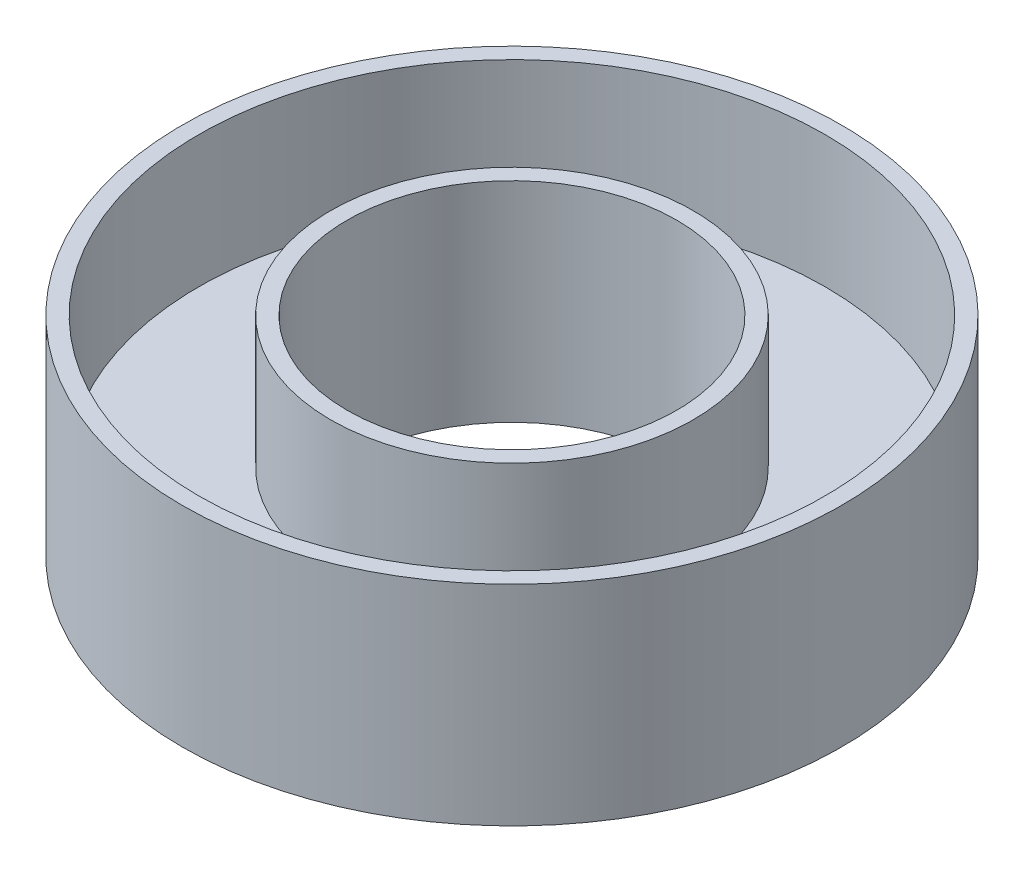
SolidWorks part; units mm, degrees
ref_plane "Front Plane" through (0, 0, 0) normal (0, 0, 1) x (1, 0, 0)
ref_plane "Top Plane" through (0, 0, 0) normal (0, 1, 0) x (1, 0, 0)
ref_plane "Right Plane" through (0, 0, 0) normal (1, 0, 0) x (0, 0, -1)
sketch "Sketch1" plane through (0, 0, 0) normal (0, 1, 0) x (1, 0, 0)
  circle A0 centre (0, 0) radius 5
  circle A1 centre (0, 0) radius 2.5
  point P6 (0, 0)
  point P7 (0, 0)
  dimension "D1" = 10
  dimension "D2" = 5
extrude "Boss-Extrude1" add sketch "Sketch1" along normal blind 3.175
sketch "Sketch2" plane through (0, 3.175, 0) normal (0, 1, 0) x (1, 0, 0)
  circle A0 centre (0, 0) radius 4.75
  circle A1 centre (0, 0) radius 2.75
  dimension "D1" = 9.5
  dimension "D2" = 5.5
extrude "Cut-Extrude1" cut sketch "Sketch2" against normal blind 2
